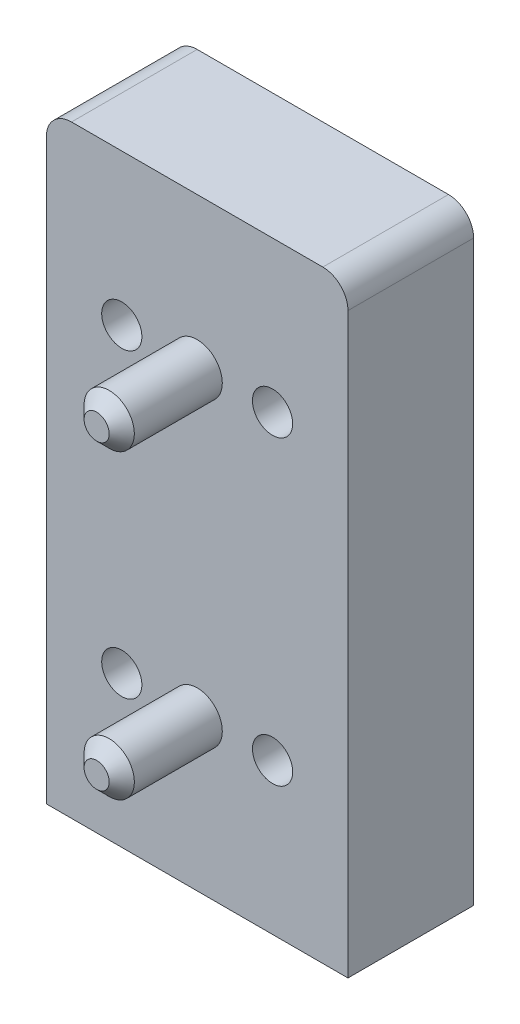
SolidWorks part; units mm, degrees
material "6061 Сплав"
ref_plane "Спереди" through (0, 0, 0) normal (0, 0, 1) x (1, 0, 0)
ref_plane "Сверху" through (0, 0, 0) normal (0, 1, 0) x (1, 0, 0)
ref_plane "Справа" through (0, 0, 0) normal (1, 0, 0) x (0, 0, -1)
sketch "Sketch1" plane through (0, 0, 0) normal (0, 0, 1) x (1, 0, 0)
  line L1 (-12, -36) -> (12, -36)
  line L2 (-12, -36) -> (-12, 10)
  line L3 (-10, 12) -> (10, 12)
  line L4 (12, -36) -> (12, 10)
  arc A0 (-12, 10) -> (-10, 12) centre (-10, 10) cw
  arc A1 (10, 12) -> (12, 10) centre (10, 10) cw
  point P0 (0, 0)
  point P10 (12, 12)
  dimension "D1" = 2
extrude "Boss-Extrude1" add sketch "Sketch1" along normal blind 10
sketch "Sketch2" plane through (0, 0, 0) normal (0, 0, -1) x (-1, 0, 0)
  line L0 (-2.14, -2.16) -> (2.14, -2.16)
  line L1 (-2.64, -1.66) -> (-2.64, 1.66)
  line L2 (-2.14, 2.16) -> (2.14, 2.16)
  line L3 (2.64, -1.66) -> (2.64, 1.66)
  line L4 (-2.64, -2.16) -> (2.64, 2.16) construction
  line L5 (-2.64, 2.16) -> (2.64, -2.16) construction
  line L6 (2.26, -25.76) -> (2.26, -22.24)
  line L7 (1.76, -26.26) -> (-1.76, -26.26)
  line L8 (-2.26, -25.76) -> (-2.26, -22.24)
  line L9 (1.76, -21.74) -> (-1.76, -21.74)
  line L10 (2.26, -26.26) -> (-2.26, -21.74) construction
  line L11 (-2.26, -26.26) -> (2.26, -21.74) construction
  circle A0 centre (4, 8) radius 1
  arc A1 (2.64, 1.66) -> (2.14, 2.16) centre (2.64, 2.16) ccw
  arc A2 (2.14, -2.16) -> (2.64, -1.66) centre (2.64, -2.16) ccw
  arc A3 (-2.64, -1.66) -> (-2.14, -2.16) centre (-2.64, -2.16) ccw
  arc A4 (-2.14, 2.16) -> (-2.64, 1.66) centre (-2.64, 2.16) ccw
  circle A5 centre (-9.027, -24.116) radius 1
  arc A6 (2.26, -22.24) -> (1.76, -21.74) centre (2.26, -21.74) ccw
  arc A7 (-1.76, -21.74) -> (-2.26, -22.24) centre (-2.26, -21.74) ccw
  arc A8 (-2.26, -25.76) -> (-1.76, -26.26) centre (-2.26, -26.26) ccw
  arc A9 (1.76, -26.26) -> (2.26, -25.76) centre (2.26, -26.26) ccw
  point P0 (0, 0)
  point P1 (0, 0)
  point P8 (-6.5, 8)
  point P9 (7.5, 8)
  point P10 (7.5, -9)
  point P11 (-6.5, -9)
  point P20 (0, -24)
  point P25 (0, -24)
  point P26 (0, -24)
  point P31 (-9.027, -17.116)
  point P32 (-9.027, -31.116)
  point P34 (7.973, -31.116)
  point P35 (7.973, -17.116)
  dimension "D11" = 5.28
  dimension "D25" = 0.5
  dimension "D1" = 8
  dimension "D2" = 9
  dimension "D3" = 6.5
  dimension "D4" = 7.5
  dimension "D5" = 6.5
  dimension "D6" = 7.5
  dimension "D7" = 9
  dimension "D8" = 8
  dimension "D9" = 3.5
  dimension "D10" = 8
  dimension "D12" = 4.32
  dimension "D13" = 4.52
  dimension "D14" = 4.52
  dimension "D15" = 9.027
  dimension "D16" = 7.116
  dimension "D17" = 6.884
  dimension "D18" = 9.027
  dimension "D19" = 7.973
  dimension "D20" = 6.884
  dimension "D21" = 7.116
  dimension "D22" = 7.973
  dimension "D23" = 9.027
  dimension "D24" = 7
extrude "Cut-Extrude1" cut sketch "Sketch2" against normal blind 0.2
sketch "Sketch3" plane through (0, 0, 10) normal (0, 0, 1) x (1, 0, 0)
  circle A0 centre (0, 0) radius 2
  circle A1 centre (0, -24) radius 2
  dimension "D1" = 24
  dimension "D2" = 4
extrude "Boss-Extrude2" add sketch "Sketch3" along normal blind 8 separate body
sketch "Sketch6" plane through (0, 0, 0) normal (0, 0, -1) x (-1, 0, 0)
  point P0 (6, 0)
  point P1 (-6, 0)
  point P2 (-6, -24)
  point P4 (6, -24)
hole_wizard "Зенковка для  винта с полупотайной головкой M31" positions "Sketch8" profile "Sketch7" countersink size "M3" standard "Ansi Metric" end condition through all
sketch "Sketch8" plane through (0, 0, 0) normal (0, 0, -1) x (-1, 0, 0)
  point P0 (6, 0)
  point P3 (-6, 0)
  point P6 (-6, -24)
  point P9 (6, -24)
sketch "Sketch7" plane through (-6, 0, 0) normal (1, 0, 0) x (0, 1, 0)
  line L0 (0, 0) -> (0, 18)
  line L1 (0, 18) -> (1.6, 18)
  line L2 (1.6, 18) -> (1.6, 1.55)
  line L3 (1.6, 1.55) -> (3.15, 0)
  line L5 (3.15, 0) -> (0, 0)
  line L6 (-1.6, 1.55) -> (-3.15, 0) construction
  line L11 (0, -6.35) -> (0, 107.95) construction
  dimension "Диаметр сквозного отверстия" = 3.2
  dimension "Глубина сквозного отверстия" = 18
  dimension "Диаметр передней зенковки" = 6.3
  dimension "Угол передней зенковки" = 90
hole_wizard "Отверстие обработанное метчиком M3x0.51" positions "Эскиз2" profile "Эскиз1" tap size "M3x0.5" standard "Ansi Metric"
sketch "Эскиз2" plane through (0, 0, 0) normal (0, 0, -1) x (-1, 0, 0)
  point P0 (-6.5, -9)
  point P3 (-9.027, -17.116)
  point P6 (7.973, -17.116)
  point P9 (7.5, -9)
  point P12 (7.5, 8)
  point P15 (-6.5, 8)
  point P18 (-9.027, -31.116)
  point P21 (7.973, -31.116)
sketch "Эскиз1" plane through (6.5, -9, 0) normal (1, 0, 0) x (0, 1, 0)
  line L0 (0, 0) -> (0, 7.2511)
  line L1 (0, 7.2511) -> (1.25, 6.5)
  line L2 (1.25, 6.5) -> (1.25, 0)
  line L5 (1.25, 0) -> (0, 0)
  line L10 (0, 7.2511) -> (-1.25, 6.5) construction
  line L11 (0, -6.35) -> (0, 107.95) construction
  dimension "Диаметр сверла" = 2.5
  dimension "Глубина сверла" = 6.5
  dimension "Угол заточки сверла" = 118
cosmetic thread "Отверстие резьбы1" parameters "D1"=5, "D2"=3
cosmetic thread "Отверстие резьбы2" parameters "D1"=5, "D2"=3
cosmetic thread "Отверстие резьбы3" parameters "D1"=5, "D2"=3
cosmetic thread "Отверстие резьбы4" parameters "D1"=5, "D2"=3
cosmetic thread "Отверстие резьбы5" parameters "D1"=5, "D2"=3
cosmetic thread "Отверстие резьбы6" parameters "D1"=5, "D2"=3
cosmetic thread "Отверстие резьбы7" parameters "D1"=5, "D2"=3
cosmetic thread "Отверстие резьбы8" parameters "D1"=5, "D2"=3
chamfer "Фаска1" distance 1 angle 45 1 edges at (2, 0, 18)
chamfer "Фаска2" distance 1 angle 45 1 edges at (2, -24, 18)
